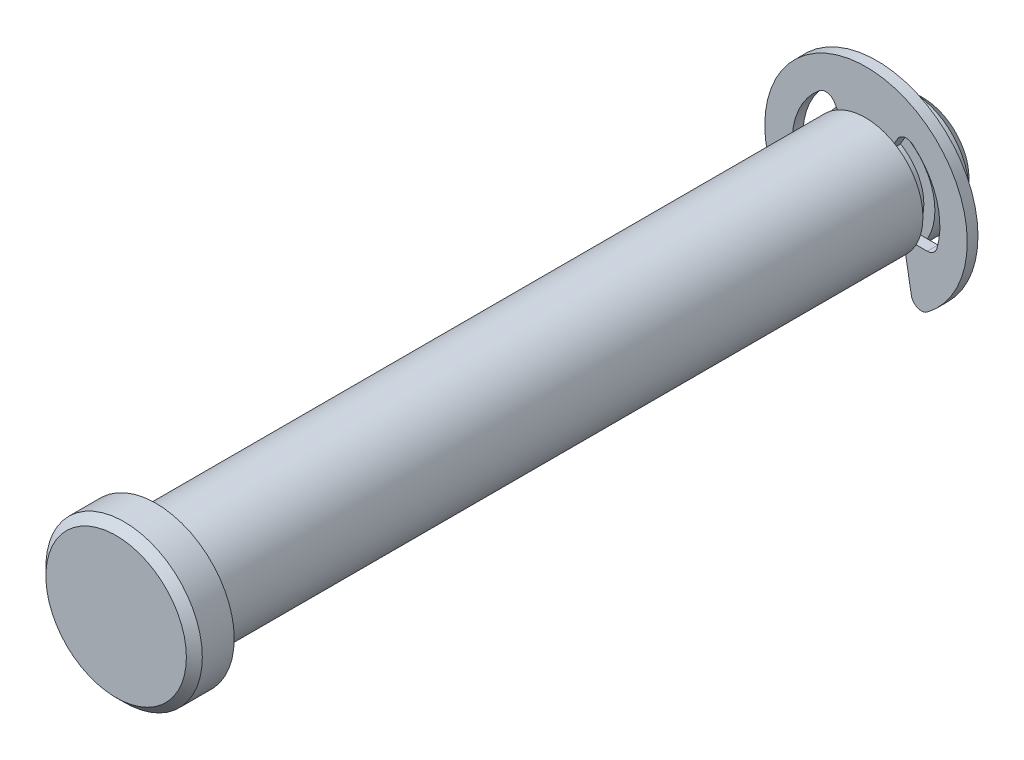
SolidWorks part; units mm, degrees
ref_plane "Front" through (0, 0, 0) normal (0, 0, 1) x (1, 0, 0)
ref_plane "Top" through (0, 0, 0) normal (0, 1, 0) x (1, 0, 0)
ref_plane "Right" through (0, 0, 0) normal (1, 0, 0) x (0, 0, -1)
sketch "Sketch2" plane through (0, 0, 0) normal (0, 0, 1) x (1, 0, 0)
  circle A0 centre (0, 0) radius 4.7625
  point P3 (0, 4.7625)
  point P4 (0, -4.7625)
  dimension "dia" = 9.525
extrude "Extrude1" add sketch "Sketch2" along normal mid plane 63.5
sketch "Sketch3" plane through (0, 0, 0) normal (1, 0, 0) x (0, 0, -1)
  line L0 (31.75, 4.7625) -> (-31.75, 4.7625) construction
  line L1 (26.9875, 4.7625) -> (27.9781, 4.7625)
  line L2 (26.9875, 4.7625) -> (26.9875, 3.8481)
  line L3 (26.9875, 3.8481) -> (27.9781, 3.8481)
  line L4 (27.9781, 4.7625) -> (27.9781, 3.8481)
  line L5 (-31.75, 4.7625) -> (-31.75, -4.7625) construction
  line L10 (27.9781, 3.8481) -> (27.9781, -3.8481) construction
  point P11 (27.9781, 0)
  point P14 (27.4828, 4.7625)
  dimension "groove wd" = 0.9906
  dimension "groove dia" = 7.6962
  dimension "usable lg" = 58.7375
revolve "Cut-Revolve1" cut sketch "Sketch3" angle 360 about axis through (0, 0, 31.75) along (0, 0, -1)
sketch "Sketch8" plane through (0, 0, 31.75) normal (0, 0, 1) x (1, 0, 0)
  circle A0 centre (0, 0) radius 6.477
  dimension "head dia" = 12.954
extrude "Extrude6" add sketch "Sketch8" along normal blind 3.302
chamfer "Chamfer2" distance 0.6604 angle 45 1 edges at (6.477, 0, 35.052)
ref_plane "Plane1" through (0, 0, -27.4828) normal (0, 0, 1) x (1, 0, 0)
sketch "Sketch4" plane through (0, 0, -27.4828) normal (0, 0, 1) x (1, 0, 0)
  line L0 (0, 3.8481) -> (0, -3.8481) construction
  circle A0 centre (0, 0) radius 8.382
  circle A1 centre (0, 0) radius 3.8481
  dimension "ring dia" = 16.764
extrude "Extrude2" add sketch "Sketch4" along normal mid plane 0.889 separate body
sketch "Sketch5" plane through (0, 0, 0) normal (0, 0, 1) x (1, 0, 0)
  line L0 (0, 8.382) -> (0, 3.8481) construction
  line L1 (-3.0575, 5.2958) -> (0, 0)
  line L2 (-5.6624, -2.3089) -> (-3.0785, -2.3089)
  line L3 (0, 0) -> (3.0575, 5.2958)
  line L4 (-3.0785, -2.3089) -> (-3.9728, -7.3807)
  line L5 (3.0785, -2.3089) -> (3.9728, -7.3807)
  line L6 (3.0785, -2.3089) -> (5.6624, -2.3089)
  arc A0 (-3.0575, 5.2958) -> (-5.6624, -2.3089) centre (0, 0) ccw
  circle A1 centre (0, 0) radius 8.382 construction
  circle A2 centre (0, 0) radius 3.8481 construction
  arc A3 (5.6624, -2.3089) -> (3.0575, 5.2958) centre (0, 0) ccw
  arc A4 (-3.9728, -7.3807) -> (3.9728, -7.3807) centre (0, 0) ccw
  circle A5 centre (0, 0) radius 3.8481 construction
  point P10 (0, 6.1151)
  dimension "D1" = 30
  dimension "D2" = 10
  dimension "D3" = 2.3089
extrude "Extrude4" cut sketch "Sketch5" against normal through all
sketch "Sketch6" plane through (0, 0, -27.0383) normal (0, 0, 1) x (1, 0, 0)
  line L0 (-1.9241, 3.3326) -> (1.9241, 3.3326)
  circle A0 centre (0, 0) radius 3.8481 construction
  arc A1 (1.9241, 3.3326) -> (-1.9241, 3.3326) centre (0, 0) ccw
extrude "Extrude5" add sketch "Sketch6" against normal up to surface (0.889 mm away) up to face at (0, 1.0514, -27.9273)
fillet "Fillet1" radius 0.8382 6 edges at (3.9728, -7.3807, -27.4828) (-3.9728, -7.3807, -27.4828) (5.6624, -2.3089, -27.4828) (3.0575, 5.2958, -27.4828) (-3.0575, 5.2958, -27.4828) (-5.6624, -2.3089, -27.4828)
chamfer "Chamfer1" distance 0.9525 angle 45 1 edges at (4.7625, 0, -31.75)
sketch "Sketch7" plane through (0, 0, 0) normal (1, 0, 0) x (0, 0, -1)
  line L0 (27.9273, 8.382) -> (27.0383, 8.382) construction
  line L1 (31.75, -4.7625) -> (31.75, 4.7625) construction
  line L2 (27.0383, -6.8329) -> (27.9273, -6.8329) construction
  line L3 (-35.052, 5.8166) -> (-35.052, -5.8166) construction
  point P0 (27.9781, -6.8329)
  point P1 (31.75, 4.7625)
  point P2 (-35.052, 6.477)
  point P6 (26.9875, 8.382)
  point P7 (31.75, -4.7625)
  point P12 (-31.75, 6.477)
  point P16 (26.9875, -6.8329)
equation "\"D1@Chamfer1\" = \"dia@Sketch2\" * .1"
equation "\"D1@Fillet1\" = \"ring dia@Sketch4\" * .05"
equation "\"D3@Sketch5\" = \"groove dia@Sketch3\" * .3"
equation "\"D1@Chamfer2\" = \"head ht@Extrude6\" * .2"
